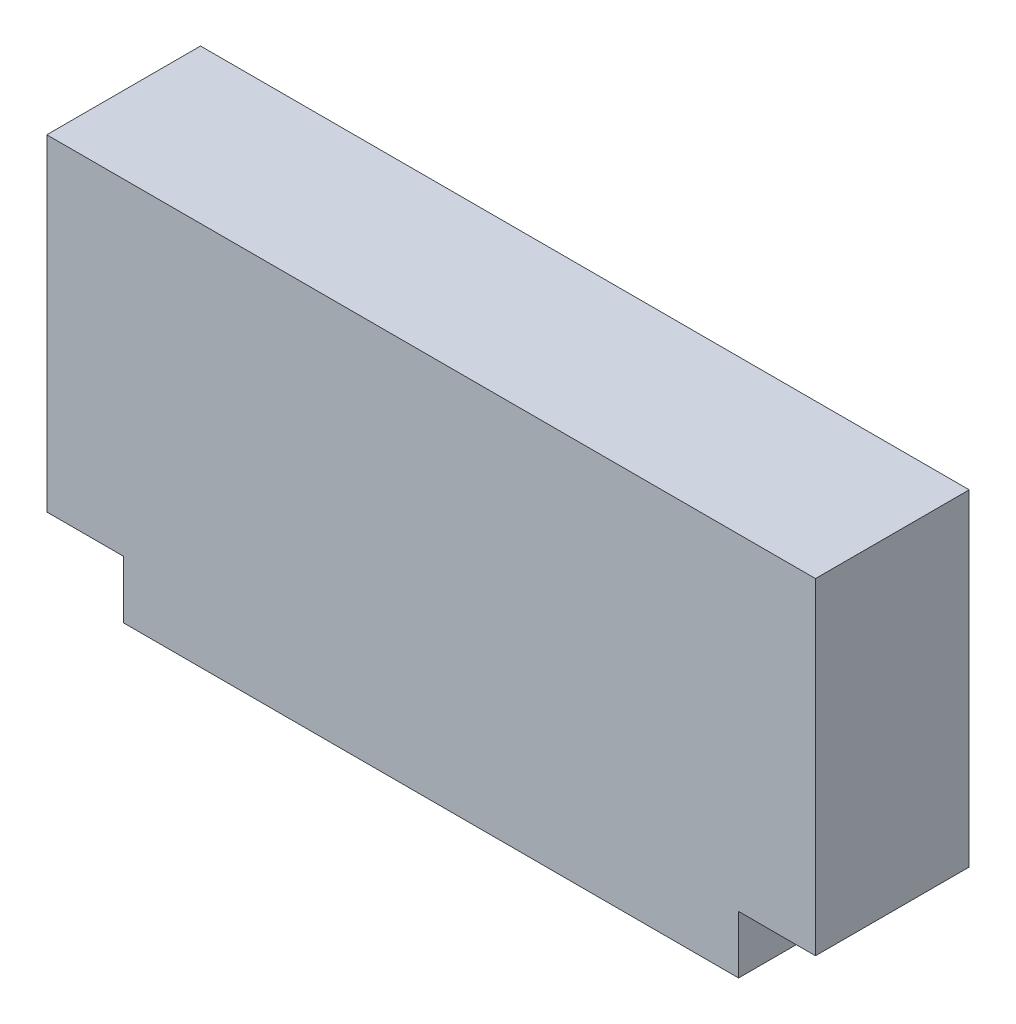
SolidWorks part; units mm, degrees
material "Стекло"
ref_plane "Спереди" through (0, 0, 0) normal (0, 0, 1) x (1, 0, 0)
ref_plane "Сверху" through (0, 0, 0) normal (0, 1, 0) x (1, 0, 0)
ref_plane "Справа" through (0, 0, 0) normal (1, 0, 0) x (0, 0, -1)
sketch "Эскиз1" plane through (0, 0, 0) normal (0, 0, 1) x (1, 0, 0)
  line L0 (0, 26.1093) -> (0, -28.0724) construction
  line L1 (-39.5878, 3) -> (32.6873, 3) construction
  line L2 (-16, 0) -> (16, 0)
  line L3 (-20, 3) -> (-20, 20)
  line L4 (-20, 20) -> (20, 20)
  line L5 (20, 3) -> (20, 20)
  line L6 (-20, 3) -> (-16, 3)
  line L7 (-16, 3) -> (-16, 0)
  line L8 (20, 3) -> (16, 3)
  line L9 (16, 3) -> (16, 0)
  dimension "D1" = 4
  dimension "D2" = 4
  dimension "D3" = 3
  dimension "D5" = 20
extrude "Бобышка-Вытянуть1" add sketch "Эскиз1" along normal blind 8
